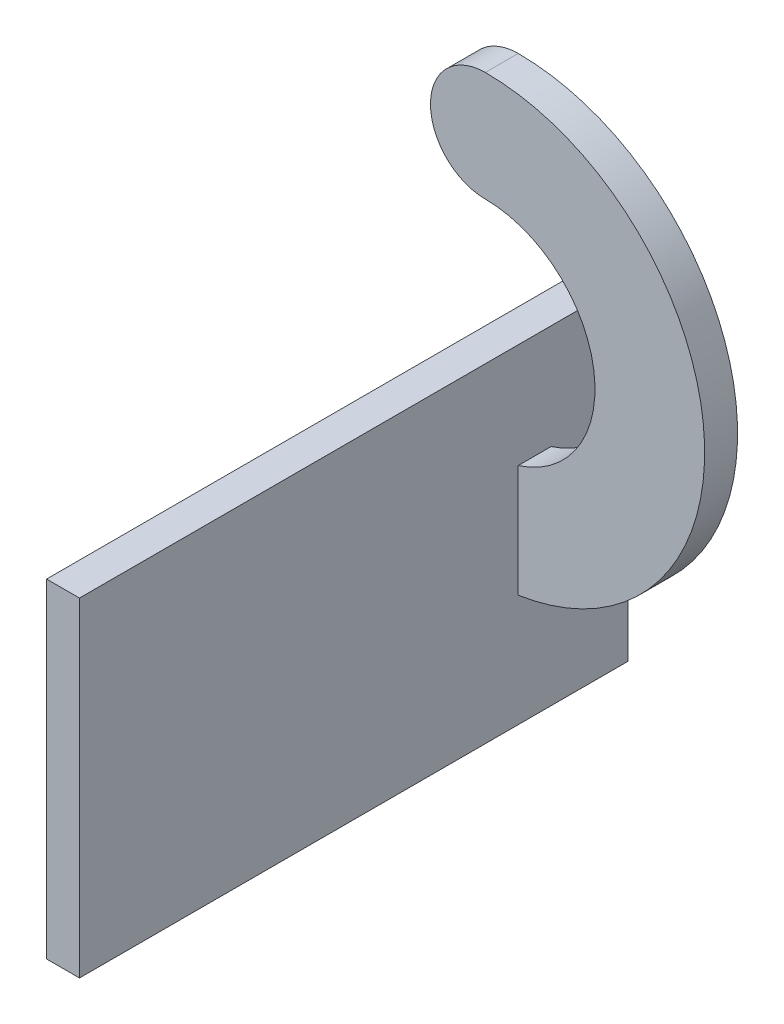
SolidWorks part; units mm, degrees
ref_plane "Front Plane" through (0, 0, 0) normal (0, 0, 1) x (1, 0, 0)
ref_plane "Top Plane" through (0, 0, 0) normal (0, 1, 0) x (1, 0, 0)
ref_plane "Right Plane" through (0, 0, 0) normal (1, 0, 0) x (0, 0, -1)
sketch "Sketch1" plane through (0, 0, 0) normal (0, 0, 1) x (1, 0, 0)
  line L0 (0, 10) -> (0, 20)
  line L1 (0, -10) -> (0, -20)
  circle A0 centre (0, 0) radius 20
  circle A1 centre (0, 0) radius 10
  circle A2 centre (0, 15) radius 5
  dimension "D1" = 40
  dimension "D2" = 20
extrude "Boss-Extrude1" add sketch "Sketch1" along normal blind 3 contours L0 A2 | L0 A2 | A2 A1 L1 A0
sketch "Sketch2" plane through (0, 0, 0) normal (-1, 0, 0) x (0, 0, 1)
  line L1 (0, -10) -> (3, -10)
  line L2 (0, -10) -> (0, -20)
  line L3 (0, -20) -> (3, -20)
  line L4 (3, -10) -> (3, -20)
extrude "Boss-Extrude2" add sketch "Sketch2" against normal blind 3
sketch "Sketch3" plane through (0, -20, 0) normal (0, -1, 0) x (-1, 0, 0)
  line L1 (0, 0) -> (-3, 0)
  line L2 (0, 0) -> (0, -3)
  line L3 (0, -3) -> (-3, -3)
  line L4 (-3, 0) -> (-3, -3)
extrude "Boss-Extrude3" add sketch "Sketch3" against normal blind 20
sketch "Sketch4" plane through (0, -20, 0) normal (0, -1, 0) x (1, 0, 0)
  line L1 (0, 0) -> (3, 0)
  line L2 (0, 0) -> (0, 3)
  line L3 (0, 3) -> (3, 3)
  line L4 (3, 0) -> (3, 3)
extrude "Boss-Extrude4" add sketch "Sketch4" along normal blind 10
sketch "Sketch5" plane through (0, 0, 3) normal (0, 0, 1) x (1, 0, 0)
  line L1 (0, 0) -> (3, 0)
  line L2 (0, 0) -> (0, -30)
  line L3 (0, -30) -> (3, -30)
  line L4 (3, 0) -> (3, -30)
extrude "Boss-Extrude5" add sketch "Sketch5" along normal blind 40
sketch "Sketch6" plane through (0, 0, 0) normal (0, 0, -1) x (-1, 0, 0)
  line L1 (0, 0) -> (-3, 0)
  line L2 (0, 0) -> (0, -30)
  line L3 (0, -30) -> (-3, -30)
  line L4 (-3, 0) -> (-3, -30)
extrude "Boss-Extrude6" add sketch "Sketch6" along normal blind 7
